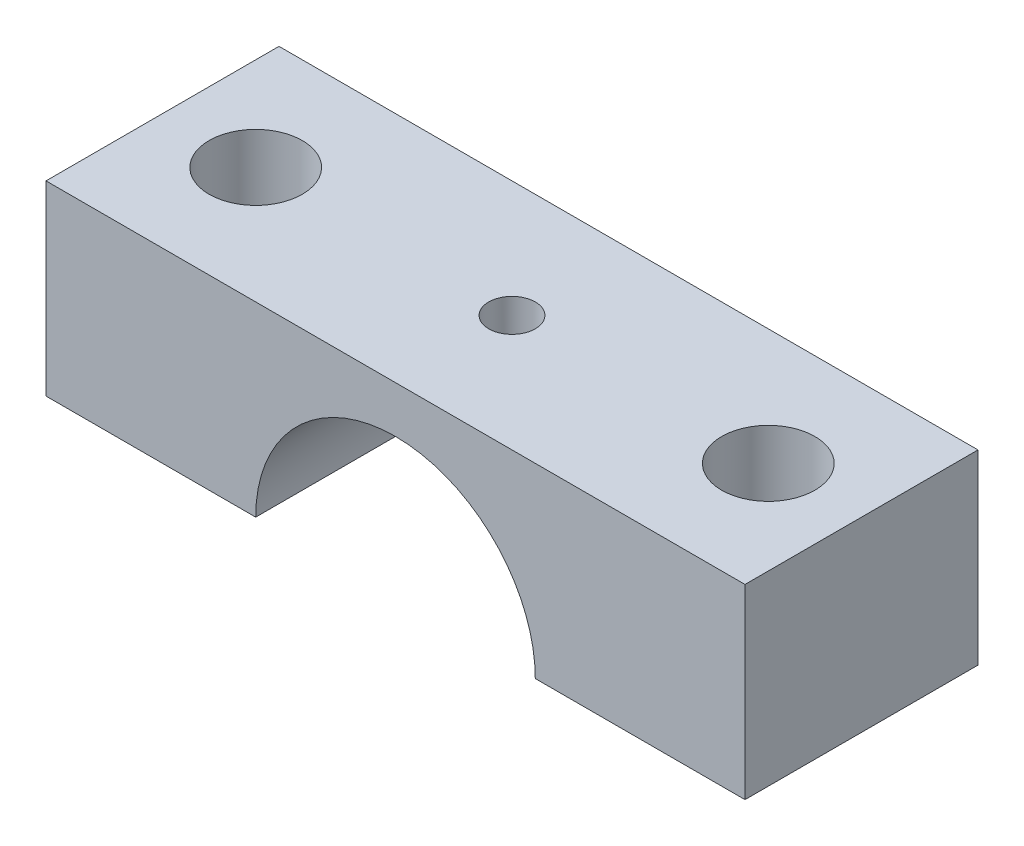
SolidWorks part; units mm, degrees
ref_plane "Front Plane" through (0, 0, 0) normal (0, 0, 1) x (1, 0, 0)
ref_plane "Top Plane" through (0, 0, 0) normal (0, 1, 0) x (1, 0, 0)
ref_plane "Right Plane" through (0, 0, 0) normal (1, 0, 0) x (0, 0, -1)
sketch "Sketch1" plane through (0, 0, 0) normal (0, 1, 0) x (1, 0, 0)
  line L0 (11, 0) -> (-11, 0) construction
  line L1 (-15, 5) -> (15, 5)
  line L2 (-15, 5) -> (-15, -5)
  line L3 (-15, -5) -> (15, -5)
  line L4 (15, 5) -> (15, -5)
  line L5 (-15, 5) -> (15, -5) construction
  line L6 (-15, -5) -> (15, 5) construction
  circle A0 centre (-11, 0) radius 2
  circle A1 centre (11, 0) radius 2
  circle A2 centre (0, 0) radius 1
  point P0 (0, 0)
  point P9 (0, 0)
  dimension "D4" = 4
  dimension "D1" = 30
  dimension "D2" = 10
  dimension "D3" = 22
extrude "Boss-Extrude1" add sketch "Sketch1" along normal blind 8
sketch "Sketch2" plane through (0, 0, 0) normal (0, 0, 1) x (1, 0, 0)
  circle A0 centre (0, 0) radius 6
  dimension "D1" = 12
extrude "Cut-Extrude1" cut sketch "Sketch2" against normal through all both and the other way through all
